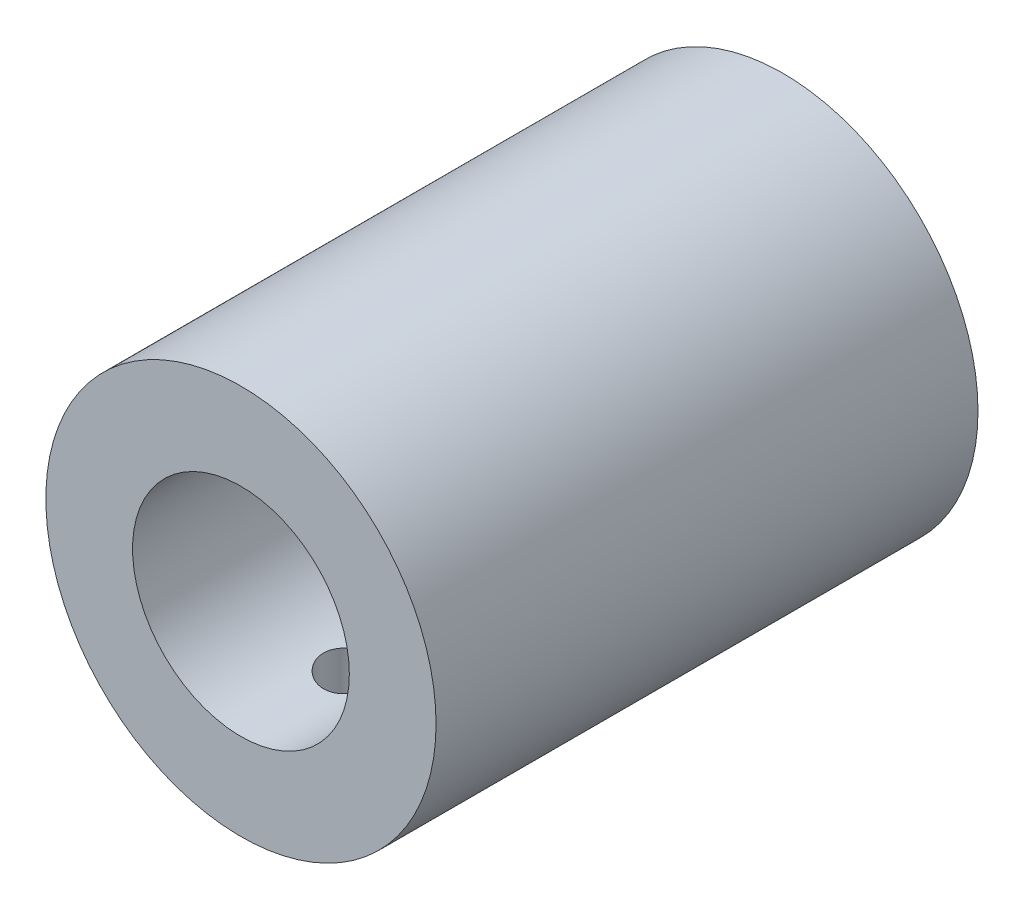
SolidWorks part; units mm, degrees
ref_plane "Front Plane" through (0, 0, 0) normal (0, 0, 1) x (1, 0, 0)
ref_plane "Top Plane" through (0, 0, 0) normal (0, 1, 0) x (1, 0, 0)
ref_plane "Right Plane" through (0, 0, 0) normal (1, 0, 0) x (0, 0, -1)
sketch "Sketch1" plane through (0, 0, 0) normal (0, 0, 1) x (1, 0, 0)
  circle A0 centre (0, 0) radius 9
  circle A1 centre (0, 0) radius 3
  dimension "D1" = 18
  dimension "D2" = 6
extrude "Boss-Extrude1" add sketch "Sketch1" along normal blind 25
sketch "Sketch2" plane through (0, 0, 25) normal (0, 0, 1) x (1, 0, 0)
  circle A0 centre (0, 0) radius 5
  dimension "D1" = 10
extrude "Cut-Extrude1" cut sketch "Sketch2" against normal blind 12.446
sketch "Sketch3" plane through (0, 0, 0) normal (0, 1, 0) x (1, 0, 0)
  line L0 (-9, -25) -> (9, -25) construction
  circle A0 centre (0, -5.08) radius 1.27
  circle A1 centre (0, -19.92) radius 1.27
  dimension "D1" = 2.54
  dimension "D2" = 2.54
  dimension "D3" = 5.08
  dimension "D4" = 5.08
extrude "Cut-Extrude2" cut sketch "Sketch3" against normal blind 12.446
